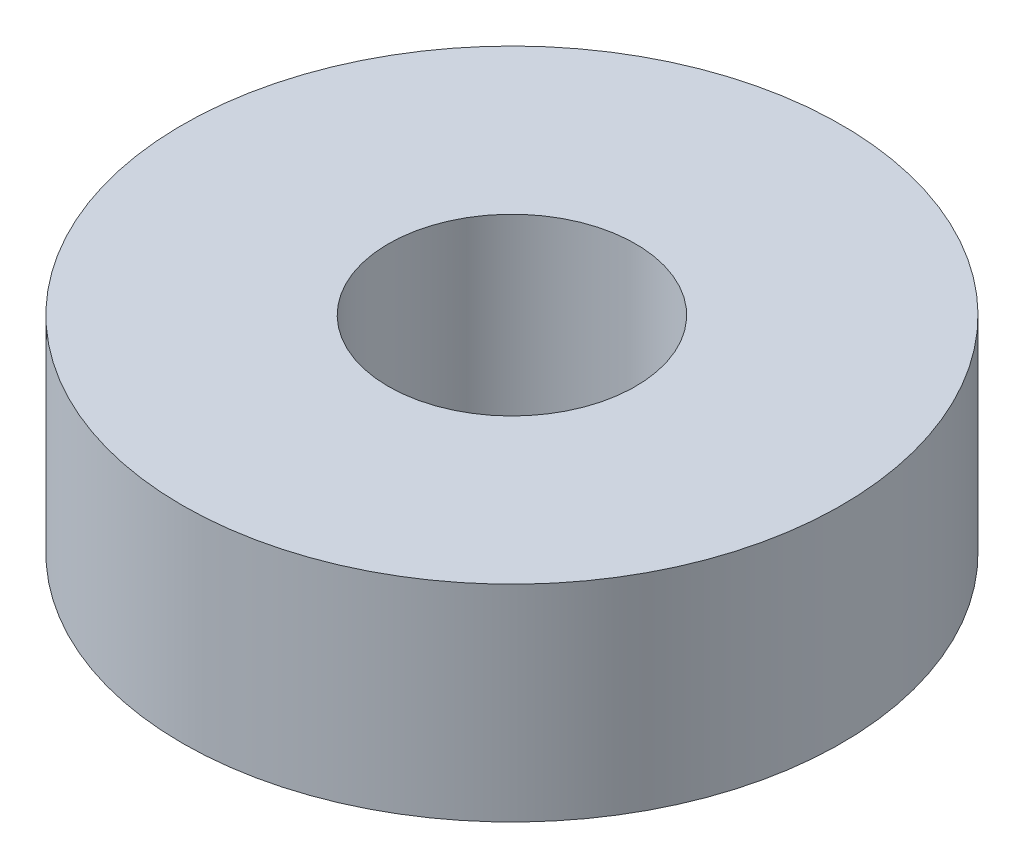
SolidWorks part; units mm, degrees
material "不锈钢 (铁素体)"
ref_plane "前视基准面" through (0, 0, 0) normal (0, 0, 1) x (1, 0, 0)
ref_plane "上视基准面" through (0, 0, 0) normal (0, 1, 0) x (1, 0, 0)
ref_plane "右视基准面" through (0, 0, 0) normal (1, 0, 0) x (0, 0, -1)
sketch "草图1" plane through (0, 0, 0) normal (0, 1, 0) x (1, 0, 0)
  circle A0 centre (0, 0) radius 1.5
  circle A1 centre (0, 0) radius 4
  dimension "D1" = 8
  dimension "D2" = 3
extrude "凸台-拉伸1" add sketch "草图1" along normal blind 2.5
